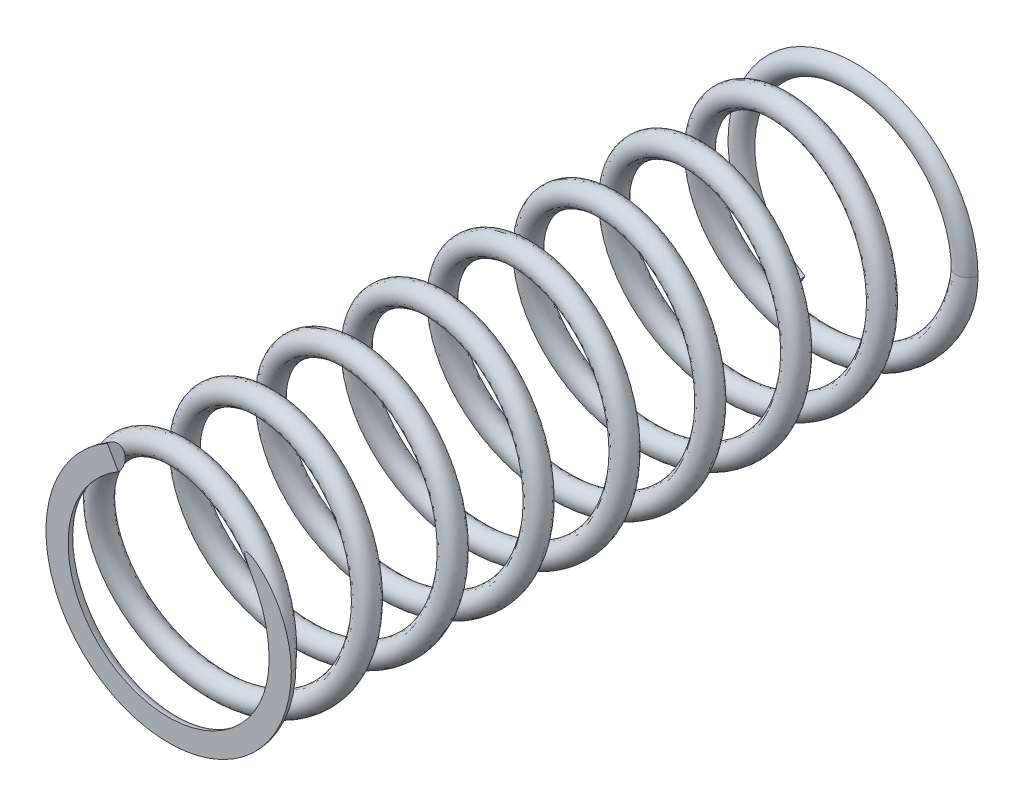
SolidWorks part; units mm, degrees
material "Alloy Steel"
ref_plane "X-Y Datum" through (0, 0, 0) normal (0, 0, 1) x (1, 0, 0)
ref_plane "X-Z Datum" through (0, 0, 0) normal (0, 1, 0) x (1, 0, 0)
ref_plane "Y-Z Datum" through (0, 0, 0) normal (1, 0, 0) x (0, 0, -1)
sketch "Sketch2" plane through (0, 0, 0) normal (0, 0, 1) x (1, 0, 0)
  circle A0 centre (0, 0) radius 18.15 construction
  circle A1 centre (0, 0) radius 20.15
  dimension "D1" = 36.3
  dimension "D2" = 2
curve "Helix/Spiral1" pitch 15.5 height 124 turns 8
ref_plane "Cap Plane" through (0, 0, 124) normal (0, 0, 1) x (1, 0, 0)
sketch "Sketch10" plane through (0, 0, 124) normal (0, 0, 1) x (1, 0, 0)
  circle A3 centre (0, 0) radius 20.15 construction
  circle A4 centre (0, 0) radius 20.15 construction
  arc A5 (20.15, 0) -> (-10.075, 17.4504) centre (0, 0) cw
  dimension "D1" = 120
sweep "Sweep1" add path "Helix/Spiral1" circular profile diameter 4 parameters "D3"=4
sweep "Sweep2" add path "Sketch10" circular profile diameter 4 parameters "D3"=4
sketch "Sketch41" plane through (0, 0, 124) normal (0, 0, 1) x (1, 0, 0)
  circle A0 centre (0, 0) radius 25
  dimension "D1" = 50
extrude "Cut-Extrude1" cut sketch "Sketch41" along normal through all
sketch "Sketch42" plane through (0, 0, 0) normal (0, 0, 1) x (1, 0, 0)
  circle A0 centre (0, 0) radius 20.15 construction
  circle A1 centre (0, 0) radius 20.15 construction
  arc A2 (20.15, 0) -> (-10.075, -17.4504) centre (0, 0) ccw
  dimension "D1" = 120
sweep "Sweep3" add path "Sketch42" circular profile diameter 4 parameters "D3"=4
sketch "Sketch55" plane through (0, 0, 0) normal (0, 0, 1) x (1, 0, 0)
  circle A0 centre (0, 0) radius 25 construction
  circle A1 centre (0, 0) radius 25
extrude "Cut-Extrude2" cut sketch "Sketch55" against normal through all
